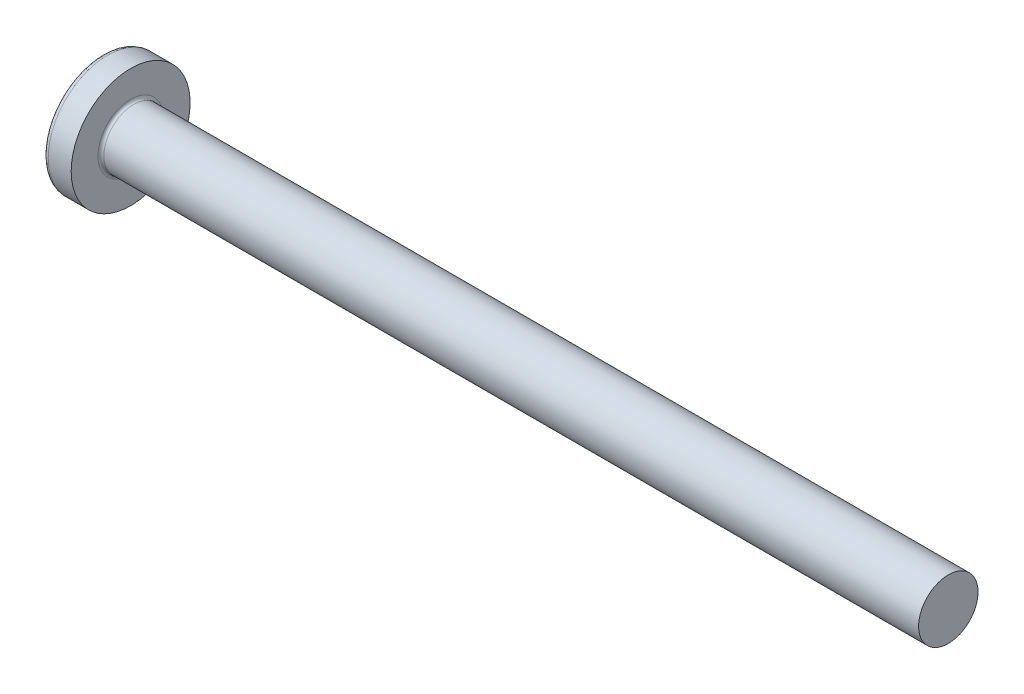
SolidWorks part; units mm, degrees
ref_plane "Plane1" through (0, 0, 0) normal (0, 0, 1) x (1, 0, 0)
ref_plane "Plane2" through (0, 0, 0) normal (0, 1, 0) x (1, 0, 0)
ref_plane "Plane3" through (0, 0, 0) normal (1, 0, 0) x (0, 0, -1)
sketch "BodySke" plane through (0, 0, 0) normal (0, 0, 1) x (1, 0, 0)
  line L0 (3.1, 2) -> (3.1, 4)
  line L1 (3.45, 6.35) -> (3.45, -3.175) construction
  line L2 (-25.4, 0) -> (127, 0) construction
  line L3 (58.1, 0) -> (0, 0)
  line L4 (3.1, 2) -> (58.1, 2)
  line L5 (58.1, 2) -> (58.1, 0)
  line L6 (1.5553, 4) -> (3.1, 4)
  line L8 (3.1, 6.35) -> (3.1, -3.175) construction
  arc A0 (1.2654, 3.8534) -> (0, 0) centre (6.5, 0) ccw
  arc A2 (1.2654, 3.8534) -> (1.5553, 4) centre (1.5553, 3.64) cw
  dimension "Head_crown_rad" = 6.5
  dimension "Head_fillet_rad" = 0.36
  dimension "Length" = 55
  dimension "Head_ht" = 3.1
  dimension "Head_dia" = 8
  dimension "Advance" = 0.7
  dimension "Thread_nom" = 55
  dimension "Diameter" = 4
revolve "Base-Revolve" add sketch "BodySke"
cosmetic thread "ThreadCosmetic" [suppressed]
fillet "Fillet1" radius 0.2 1 edges at (3.1, 0, 2)
sketch "Sketch3" plane through (0, 0, 0) normal (1, 0, 0) x (0, 0, -1)
  line L0 (0.515, -2.15) -> (-0.515, -2.15)
  line L1 (0.515, -2.15) -> (0.515, 2.15)
  line L2 (-0.515, 2.15) -> (0.515, 2.15)
  line L3 (-0.515, 2.15) -> (-0.515, -2.15)
  dimension "Cross_dia" = 4.3
  dimension "D1" = 2.15
  dimension "Cross_width" = 1.03
  dimension "D2" = 0.515
ref_plane "Plane4" through (2.34, 0, 0) normal (1, 0, 0) x (0, 0, -1)
sketch "Sketch4" plane through (2.34, 0, 0) normal (1, 0, 0) x (0, 0, -1)
  line L0 (0.515, -0.9833) -> (-0.515, -0.9833)
  line L1 (0.515, -0.9833) -> (0.515, 0.9833)
  line L2 (-0.515, 0.9833) -> (0.515, 0.9833)
  line L3 (-0.515, 0.9833) -> (-0.515, -0.9833)
  dimension "D1" = 1.03
  dimension "D2" = 1.9666
  dimension "D3" = 0.515
  dimension "D4" = 0.9833
loft "Recess" cut profiles "Sketch3", "Sketch4"
pattern_circular "RecPat" count 2 every 90 about axis through (0, 0, 0) along (1, 0, 0) of "Recess"
sketch "RecCorSke" plane through (0, 0, 0) normal (0, 0, 1) x (1, 0, 0)
  line L0 (-3.175, 0) -> (15.875, 0) construction
  line L1 (-25.4, 0) -> (127, 0) construction
  line L2 (0, 0) -> (0, 1.0146)
  line L3 (0, 1.0146) -> (2.34, 0.851)
  line L4 (2.34, 0.851) -> (2.6165, 0)
  line L5 (2.6165, 0) -> (0, 0)
  dimension "Diameter" = 1.702
  dimension "Depth" = 2.34
  dimension "Draft_angle" = 4
  dimension "Bottom_angle" = 18
revolve "RecessCore" cut sketch "RecCorSke" angle 360 about L0
sketch "ThdSchSke" plane through (0, 0, 0) normal (0, 0, 1) x (1, 0, 0)
  line L0 (4.5, -1.61) -> (4.2269, -2)
  line L1 (4.5, -1.61) -> (4.7731, -2)
  line L2 (4.7731, -2) -> (4.7731, -2.5)
  line L3 (-3.175, 0) -> (5.1513, 0) construction
  line L5 (4.7731, -2.5) -> (4.2269, -2.5)
  line L6 (4.2269, -2.5) -> (4.2269, -2)
  dimension "Diameter" = 4
  dimension "SideAngle" = 55
  dimension "VeeAngle" = 70
  dimension "Thread_minor" = 3.22
  dimension "Overcut" = 5
  dimension "Start" = 4.5
revolve "ThreadSchematic" [suppressed] cut sketch "ThdSchSke" angle 360 about L3
pattern_linear "ThdSchPat" [suppressed]
equation "\"D1@Sketch3\" = \"Cross_dia@Sketch3\" / 2"
equation "\"D2@Sketch3\" = \"Cross_width@Sketch3\" / 2"
equation "\"Depth@RecCorSke\" = \"Cross_depth@Plane4\""
equation "\"D1@Sketch4\" = \"Cross_width@Sketch3\""
equation "\"D2@Sketch4\" = \"Cross_dia@Sketch3\" - 2.0 * \"Cross_depth@Plane4\" * tan(26.5  * 0.017453292)"
equation "\"D3@Sketch4\" = \"D1@Sketch4\" / 2"
equation "\"D4@Sketch4\" = \"D2@Sketch4\" / 2"
equation "\"Thread_length@ThreadCosmetic\" = ((sgn( (\"Length@BodySke\" - \"Advance@BodySke\" * 2.0 ) - \"Thread_nom@BodySke\" )-1)*( (\"Length@BodySke\" - \"Advance@BodySke\" * 2.0 ) - \"Thread_nom@BodySke\" ))/-2+ \"Thread_nom@BodySke\""
equation "\"Thread_minor@ThdSchSke\" = \"Thread_minor@ThreadCosmetic\""
equation "\"Diameter@ThdSchSke\" = \"Diameter@BodySke\""
equation "\"Overcut@ThdSchSke\" = \"Diameter@BodySke\" * 1.25"
equation "\"Start@ThdSchSke\" = \"Head_ht@BodySke\" + \"Length@BodySke\" - \"Thread_length@ThreadCosmetic\"  '---Non-countersunk---"
equation "\"Num_threads@ThdSchPat\" = int( \"Thread_length@ThreadCosmetic\" / \"Advance@BodySke\" + 0.999 )  + 1"
equation "\"Advance@ThdSchPat\" = \"Thread_length@ThreadCosmetic\" /  (\"Num_threads@ThdSchPat\" - 1) 'relax it"
